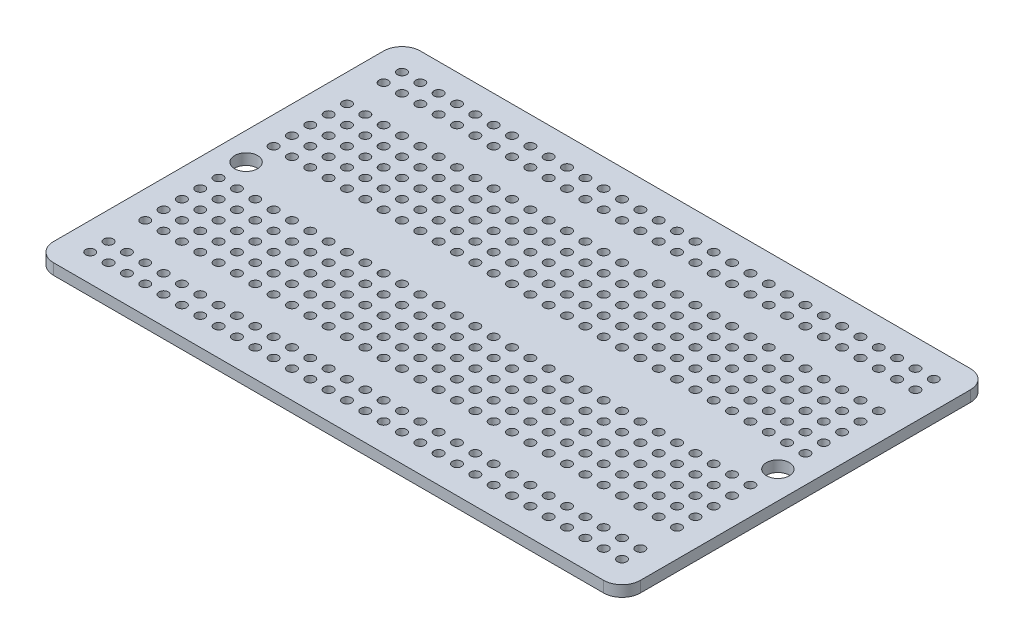
SolidWorks part; units mm, degrees
ref_plane "Front Plane" through (0, 0, 0) normal (0, 0, 1) x (1, 0, 0)
ref_plane "Top Plane" through (0, 0, 0) normal (0, 1, 0) x (1, 0, 0)
ref_plane "Right Plane" through (0, 0, 0) normal (1, 0, 0) x (0, 0, -1)
sketch "Sketch1" plane through (0, 0, 0) normal (0, 1, 0) x (1, 0, 0)
  line L0 (3.81, 46.99) -> (6.35, 46.99) construction
  line L1 (2.54, 0) -> (78.74, 0)
  line L2 (0, 2.54) -> (0, 48.26)
  line L3 (2.54, 50.8) -> (78.74, 50.8)
  line L4 (81.28, 2.54) -> (81.28, 48.26)
  line L5 (3.81, 44.45) -> (6.35, 44.45) construction
  line L6 (3.81, 41.91) -> (6.35, 41.91) construction
  line L7 (3.81, 39.37) -> (6.35, 39.37) construction
  line L8 (3.81, 36.83) -> (6.35, 36.83) construction
  line L9 (3.81, 34.29) -> (6.35, 34.29) construction
  line L10 (3.81, 31.75) -> (6.35, 31.75) construction
  line L11 (3.81, 29.21) -> (6.35, 29.21) construction
  line L12 (3.81, 26.67) -> (6.35, 26.67) construction
  line L13 (3.81, 24.13) -> (6.35, 24.13) construction
  line L14 (3.81, 21.59) -> (6.35, 21.59) construction
  line L15 (3.81, 19.05) -> (6.35, 19.05) construction
  line L16 (3.81, 16.51) -> (6.35, 16.51) construction
  line L17 (3.81, 13.97) -> (6.35, 13.97) construction
  line L18 (3.81, 11.43) -> (6.35, 11.43) construction
  line L19 (3.81, 8.89) -> (6.35, 8.89) construction
  line L20 (3.81, 6.35) -> (6.35, 6.35) construction
  line L21 (3.81, 3.81) -> (6.35, 3.81) construction
  line L22 (3.81, 46.99) -> (3.81, 44.45) construction
  arc A0 (78.74, 50.8) -> (81.28, 48.26) centre (78.74, 48.26) cw
  arc A1 (78.74, 0) -> (81.28, 2.54) centre (78.74, 2.54) ccw
  arc A2 (2.54, 0) -> (0, 2.54) centre (2.54, 2.54) cw
  arc A3 (0, 48.26) -> (2.54, 50.8) centre (2.54, 48.26) cw
  circle A4 centre (3.81, 46.99) radius 0.635
  circle A5 centre (6.35, 46.99) radius 0.635
  circle A6 centre (8.89, 46.99) radius 0.635
  circle A7 centre (11.43, 46.99) radius 0.635
  circle A8 centre (13.97, 46.99) radius 0.635
  circle A9 centre (16.51, 46.99) radius 0.635
  circle A10 centre (19.05, 46.99) radius 0.635
  circle A11 centre (21.59, 46.99) radius 0.635
  circle A12 centre (24.13, 46.99) radius 0.635
  circle A13 centre (26.67, 46.99) radius 0.635
  circle A14 centre (29.21, 46.99) radius 0.635
  circle A15 centre (31.75, 46.99) radius 0.635
  circle A16 centre (34.29, 46.99) radius 0.635
  circle A17 centre (36.83, 46.99) radius 0.635
  circle A18 centre (39.37, 46.99) radius 0.635
  circle A19 centre (41.91, 46.99) radius 0.635
  circle A20 centre (44.45, 46.99) radius 0.635
  circle A21 centre (46.99, 46.99) radius 0.635
  circle A22 centre (49.53, 46.99) radius 0.635
  circle A23 centre (52.07, 46.99) radius 0.635
  circle A24 centre (54.61, 46.99) radius 0.635
  circle A25 centre (57.15, 46.99) radius 0.635
  circle A26 centre (59.69, 46.99) radius 0.635
  circle A27 centre (62.23, 46.99) radius 0.635
  circle A28 centre (64.77, 46.99) radius 0.635
  circle A29 centre (67.31, 46.99) radius 0.635
  circle A30 centre (69.85, 46.99) radius 0.635
  circle A31 centre (72.39, 46.99) radius 0.635
  circle A32 centre (74.93, 46.99) radius 0.635
  circle A33 centre (77.47, 46.99) radius 0.635
  circle A34 centre (3.81, 44.45) radius 0.635
  circle A35 centre (6.35, 44.45) radius 0.635
  circle A36 centre (8.89, 44.45) radius 0.635
  circle A37 centre (11.43, 44.45) radius 0.635
  circle A38 centre (13.97, 44.45) radius 0.635
  circle A39 centre (16.51, 44.45) radius 0.635
  circle A40 centre (19.05, 44.45) radius 0.635
  circle A41 centre (21.59, 44.45) radius 0.635
  circle A42 centre (24.13, 44.45) radius 0.635
  circle A43 centre (26.67, 44.45) radius 0.635
  circle A44 centre (29.21, 44.45) radius 0.635
  circle A45 centre (31.75, 44.45) radius 0.635
  circle A46 centre (34.29, 44.45) radius 0.635
  circle A47 centre (36.83, 44.45) radius 0.635
  circle A48 centre (39.37, 44.45) radius 0.635
  circle A49 centre (41.91, 44.45) radius 0.635
  circle A50 centre (44.45, 44.45) radius 0.635
  circle A51 centre (46.99, 44.45) radius 0.635
  circle A52 centre (49.53, 44.45) radius 0.635
  circle A53 centre (52.07, 44.45) radius 0.635
  circle A54 centre (54.61, 44.45) radius 0.635
  circle A55 centre (57.15, 44.45) radius 0.635
  circle A56 centre (59.69, 44.45) radius 0.635
  circle A57 centre (62.23, 44.45) radius 0.635
  circle A58 centre (64.77, 44.45) radius 0.635
  circle A59 centre (67.31, 44.45) radius 0.635
  circle A60 centre (69.85, 44.45) radius 0.635
  circle A61 centre (72.39, 44.45) radius 0.635
  circle A62 centre (74.93, 44.45) radius 0.635
  circle A63 centre (77.47, 44.45) radius 0.635
  circle A64 centre (3.81, 41.91) radius 0.635 [skipped]
  circle A65 centre (6.35, 41.91) radius 0.635 [skipped]
  circle A66 centre (8.89, 41.91) radius 0.635 [skipped]
  circle A67 centre (11.43, 41.91) radius 0.635 [skipped]
  circle A68 centre (13.97, 41.91) radius 0.635 [skipped]
  circle A69 centre (16.51, 41.91) radius 0.635 [skipped]
  circle A70 centre (19.05, 41.91) radius 0.635 [skipped]
  circle A71 centre (21.59, 41.91) radius 0.635 [skipped]
  circle A72 centre (24.13, 41.91) radius 0.635 [skipped]
  circle A73 centre (26.67, 41.91) radius 0.635 [skipped]
  circle A74 centre (29.21, 41.91) radius 0.635 [skipped]
  circle A75 centre (31.75, 41.91) radius 0.635 [skipped]
  circle A76 centre (34.29, 41.91) radius 0.635 [skipped]
  circle A77 centre (36.83, 41.91) radius 0.635 [skipped]
  circle A78 centre (39.37, 41.91) radius 0.635 [skipped]
  circle A79 centre (41.91, 41.91) radius 0.635 [skipped]
  circle A80 centre (44.45, 41.91) radius 0.635 [skipped]
  circle A81 centre (46.99, 41.91) radius 0.635 [skipped]
  circle A82 centre (49.53, 41.91) radius 0.635 [skipped]
  circle A83 centre (52.07, 41.91) radius 0.635 [skipped]
  circle A84 centre (54.61, 41.91) radius 0.635 [skipped]
  circle A85 centre (57.15, 41.91) radius 0.635 [skipped]
  circle A86 centre (59.69, 41.91) radius 0.635 [skipped]
  circle A87 centre (62.23, 41.91) radius 0.635 [skipped]
  circle A88 centre (64.77, 41.91) radius 0.635 [skipped]
  circle A89 centre (67.31, 41.91) radius 0.635 [skipped]
  circle A90 centre (69.85, 41.91) radius 0.635 [skipped]
  circle A91 centre (72.39, 41.91) radius 0.635 [skipped]
  circle A92 centre (74.93, 41.91) radius 0.635 [skipped]
  circle A93 centre (77.47, 41.91) radius 0.635 [skipped]
  circle A94 centre (3.81, 39.37) radius 0.635
  circle A95 centre (6.35, 39.37) radius 0.635
  circle A96 centre (8.89, 39.37) radius 0.635
  circle A97 centre (11.43, 39.37) radius 0.635
  circle A98 centre (13.97, 39.37) radius 0.635
  circle A99 centre (16.51, 39.37) radius 0.635
  circle A100 centre (19.05, 39.37) radius 0.635
  circle A101 centre (21.59, 39.37) radius 0.635
  circle A102 centre (24.13, 39.37) radius 0.635
  circle A103 centre (26.67, 39.37) radius 0.635
  circle A104 centre (29.21, 39.37) radius 0.635
  circle A105 centre (31.75, 39.37) radius 0.635
  circle A106 centre (34.29, 39.37) radius 0.635
  circle A107 centre (36.83, 39.37) radius 0.635
  circle A108 centre (39.37, 39.37) radius 0.635
  circle A109 centre (41.91, 39.37) radius 0.635
  circle A110 centre (44.45, 39.37) radius 0.635
  circle A111 centre (46.99, 39.37) radius 0.635
  circle A112 centre (49.53, 39.37) radius 0.635
  circle A113 centre (52.07, 39.37) radius 0.635
  circle A114 centre (54.61, 39.37) radius 0.635
  circle A115 centre (57.15, 39.37) radius 0.635
  circle A116 centre (59.69, 39.37) radius 0.635
  circle A117 centre (62.23, 39.37) radius 0.635
  circle A118 centre (64.77, 39.37) radius 0.635
  circle A119 centre (67.31, 39.37) radius 0.635
  circle A120 centre (69.85, 39.37) radius 0.635
  circle A121 centre (72.39, 39.37) radius 0.635
  circle A122 centre (74.93, 39.37) radius 0.635
  circle A123 centre (77.47, 39.37) radius 0.635
  circle A124 centre (3.81, 36.83) radius 0.635
  circle A125 centre (6.35, 36.83) radius 0.635
  circle A126 centre (8.89, 36.83) radius 0.635
  circle A127 centre (11.43, 36.83) radius 0.635
  circle A128 centre (13.97, 36.83) radius 0.635
  circle A129 centre (16.51, 36.83) radius 0.635
  circle A130 centre (19.05, 36.83) radius 0.635
  circle A131 centre (21.59, 36.83) radius 0.635
  circle A132 centre (24.13, 36.83) radius 0.635
  circle A133 centre (26.67, 36.83) radius 0.635
  circle A134 centre (29.21, 36.83) radius 0.635
  circle A135 centre (31.75, 36.83) radius 0.635
  circle A136 centre (34.29, 36.83) radius 0.635
  circle A137 centre (36.83, 36.83) radius 0.635
  circle A138 centre (39.37, 36.83) radius 0.635
  circle A139 centre (41.91, 36.83) radius 0.635
  circle A140 centre (44.45, 36.83) radius 0.635
  circle A141 centre (46.99, 36.83) radius 0.635
  circle A142 centre (49.53, 36.83) radius 0.635
  circle A143 centre (52.07, 36.83) radius 0.635
  circle A144 centre (54.61, 36.83) radius 0.635
  circle A145 centre (57.15, 36.83) radius 0.635
  circle A146 centre (59.69, 36.83) radius 0.635
  circle A147 centre (62.23, 36.83) radius 0.635
  circle A148 centre (64.77, 36.83) radius 0.635
  circle A149 centre (67.31, 36.83) radius 0.635
  circle A150 centre (69.85, 36.83) radius 0.635
  circle A151 centre (72.39, 36.83) radius 0.635
  circle A152 centre (74.93, 36.83) radius 0.635
  circle A153 centre (77.47, 36.83) radius 0.635
  circle A154 centre (3.81, 34.29) radius 0.635
  circle A155 centre (6.35, 34.29) radius 0.635
  circle A156 centre (8.89, 34.29) radius 0.635
  circle A157 centre (11.43, 34.29) radius 0.635
  circle A158 centre (13.97, 34.29) radius 0.635
  circle A159 centre (16.51, 34.29) radius 0.635
  circle A160 centre (19.05, 34.29) radius 0.635
  circle A161 centre (21.59, 34.29) radius 0.635
  circle A162 centre (24.13, 34.29) radius 0.635
  circle A163 centre (26.67, 34.29) radius 0.635
  circle A164 centre (29.21, 34.29) radius 0.635
  circle A165 centre (31.75, 34.29) radius 0.635
  circle A166 centre (34.29, 34.29) radius 0.635
  circle A167 centre (36.83, 34.29) radius 0.635
  circle A168 centre (39.37, 34.29) radius 0.635
  circle A169 centre (41.91, 34.29) radius 0.635
  circle A170 centre (44.45, 34.29) radius 0.635
  circle A171 centre (46.99, 34.29) radius 0.635
  circle A172 centre (49.53, 34.29) radius 0.635
  circle A173 centre (52.07, 34.29) radius 0.635
  circle A174 centre (54.61, 34.29) radius 0.635
  circle A175 centre (57.15, 34.29) radius 0.635
  circle A176 centre (59.69, 34.29) radius 0.635
  circle A177 centre (62.23, 34.29) radius 0.635
  circle A178 centre (64.77, 34.29) radius 0.635
  circle A179 centre (67.31, 34.29) radius 0.635
  circle A180 centre (69.85, 34.29) radius 0.635
  circle A181 centre (72.39, 34.29) radius 0.635
  circle A182 centre (74.93, 34.29) radius 0.635
  circle A183 centre (77.47, 34.29) radius 0.635
  circle A184 centre (3.81, 31.75) radius 0.635
  circle A185 centre (6.35, 31.75) radius 0.635
  circle A186 centre (8.89, 31.75) radius 0.635
  circle A187 centre (11.43, 31.75) radius 0.635
  circle A188 centre (13.97, 31.75) radius 0.635
  circle A189 centre (16.51, 31.75) radius 0.635
  circle A190 centre (19.05, 31.75) radius 0.635
  circle A191 centre (21.59, 31.75) radius 0.635
  circle A192 centre (24.13, 31.75) radius 0.635
  circle A193 centre (26.67, 31.75) radius 0.635
  circle A194 centre (29.21, 31.75) radius 0.635
  circle A195 centre (31.75, 31.75) radius 0.635
  circle A196 centre (34.29, 31.75) radius 0.635
  circle A197 centre (36.83, 31.75) radius 0.635
  circle A198 centre (39.37, 31.75) radius 0.635
  circle A199 centre (41.91, 31.75) radius 0.635
  circle A200 centre (44.45, 31.75) radius 0.635
  circle A201 centre (46.99, 31.75) radius 0.635
  circle A202 centre (49.53, 31.75) radius 0.635
  circle A203 centre (52.07, 31.75) radius 0.635
  circle A204 centre (54.61, 31.75) radius 0.635
  circle A205 centre (57.15, 31.75) radius 0.635
  circle A206 centre (59.69, 31.75) radius 0.635
  circle A207 centre (62.23, 31.75) radius 0.635
  circle A208 centre (64.77, 31.75) radius 0.635
  circle A209 centre (67.31, 31.75) radius 0.635
  circle A210 centre (69.85, 31.75) radius 0.635
  circle A211 centre (72.39, 31.75) radius 0.635
  circle A212 centre (74.93, 31.75) radius 0.635
  circle A213 centre (77.47, 31.75) radius 0.635
  circle A214 centre (3.81, 29.21) radius 0.635
  circle A215 centre (6.35, 29.21) radius 0.635
  circle A216 centre (8.89, 29.21) radius 0.635
  circle A217 centre (11.43, 29.21) radius 0.635
  circle A218 centre (13.97, 29.21) radius 0.635
  circle A219 centre (16.51, 29.21) radius 0.635
  circle A220 centre (19.05, 29.21) radius 0.635
  circle A221 centre (21.59, 29.21) radius 0.635
  circle A222 centre (24.13, 29.21) radius 0.635
  circle A223 centre (26.67, 29.21) radius 0.635
  circle A224 centre (29.21, 29.21) radius 0.635
  circle A225 centre (31.75, 29.21) radius 0.635
  circle A226 centre (34.29, 29.21) radius 0.635
  circle A227 centre (36.83, 29.21) radius 0.635
  circle A228 centre (39.37, 29.21) radius 0.635
  circle A229 centre (41.91, 29.21) radius 0.635
  circle A230 centre (44.45, 29.21) radius 0.635
  circle A231 centre (46.99, 29.21) radius 0.635
  circle A232 centre (49.53, 29.21) radius 0.635
  circle A233 centre (52.07, 29.21) radius 0.635
  circle A234 centre (54.61, 29.21) radius 0.635
  circle A235 centre (57.15, 29.21) radius 0.635
  circle A236 centre (59.69, 29.21) radius 0.635
  circle A237 centre (62.23, 29.21) radius 0.635
  circle A238 centre (64.77, 29.21) radius 0.635
  circle A239 centre (67.31, 29.21) radius 0.635
  circle A240 centre (69.85, 29.21) radius 0.635
  circle A241 centre (72.39, 29.21) radius 0.635
  circle A242 centre (74.93, 29.21) radius 0.635
  circle A243 centre (77.47, 29.21) radius 0.635
  circle A244 centre (3.81, 26.67) radius 0.635 [skipped]
  circle A245 centre (6.35, 26.67) radius 0.635 [skipped]
  circle A246 centre (8.89, 26.67) radius 0.635 [skipped]
  circle A247 centre (11.43, 26.67) radius 0.635 [skipped]
  circle A248 centre (13.97, 26.67) radius 0.635 [skipped]
  circle A249 centre (16.51, 26.67) radius 0.635 [skipped]
  circle A250 centre (19.05, 26.67) radius 0.635 [skipped]
  circle A251 centre (21.59, 26.67) radius 0.635 [skipped]
  circle A252 centre (24.13, 26.67) radius 0.635 [skipped]
  circle A253 centre (26.67, 26.67) radius 0.635 [skipped]
  circle A254 centre (29.21, 26.67) radius 0.635 [skipped]
  circle A255 centre (31.75, 26.67) radius 0.635 [skipped]
  circle A256 centre (34.29, 26.67) radius 0.635 [skipped]
  circle A257 centre (36.83, 26.67) radius 0.635 [skipped]
  circle A258 centre (39.37, 26.67) radius 0.635 [skipped]
  circle A259 centre (41.91, 26.67) radius 0.635 [skipped]
  circle A260 centre (44.45, 26.67) radius 0.635 [skipped]
  circle A261 centre (46.99, 26.67) radius 0.635 [skipped]
  circle A262 centre (49.53, 26.67) radius 0.635 [skipped]
  circle A263 centre (52.07, 26.67) radius 0.635 [skipped]
  circle A264 centre (54.61, 26.67) radius 0.635 [skipped]
  circle A265 centre (57.15, 26.67) radius 0.635 [skipped]
  circle A266 centre (59.69, 26.67) radius 0.635 [skipped]
  circle A267 centre (62.23, 26.67) radius 0.635 [skipped]
  circle A268 centre (64.77, 26.67) radius 0.635 [skipped]
  circle A269 centre (67.31, 26.67) radius 0.635 [skipped]
  circle A270 centre (69.85, 26.67) radius 0.635 [skipped]
  circle A271 centre (72.39, 26.67) radius 0.635 [skipped]
  circle A272 centre (74.93, 26.67) radius 0.635 [skipped]
  circle A273 centre (77.47, 26.67) radius 0.635 [skipped]
  circle A274 centre (3.81, 24.13) radius 0.635 [skipped]
  circle A275 centre (6.35, 24.13) radius 0.635 [skipped]
  circle A276 centre (8.89, 24.13) radius 0.635 [skipped]
  circle A277 centre (11.43, 24.13) radius 0.635 [skipped]
  circle A278 centre (13.97, 24.13) radius 0.635 [skipped]
  circle A279 centre (16.51, 24.13) radius 0.635 [skipped]
  circle A280 centre (19.05, 24.13) radius 0.635 [skipped]
  circle A281 centre (21.59, 24.13) radius 0.635 [skipped]
  circle A282 centre (24.13, 24.13) radius 0.635 [skipped]
  circle A283 centre (26.67, 24.13) radius 0.635 [skipped]
  circle A284 centre (29.21, 24.13) radius 0.635 [skipped]
  circle A285 centre (31.75, 24.13) radius 0.635 [skipped]
  circle A286 centre (34.29, 24.13) radius 0.635 [skipped]
  circle A287 centre (36.83, 24.13) radius 0.635 [skipped]
  circle A288 centre (39.37, 24.13) radius 0.635 [skipped]
  circle A289 centre (41.91, 24.13) radius 0.635 [skipped]
  circle A290 centre (44.45, 24.13) radius 0.635 [skipped]
  circle A291 centre (46.99, 24.13) radius 0.635 [skipped]
  circle A292 centre (49.53, 24.13) radius 0.635 [skipped]
  circle A293 centre (52.07, 24.13) radius 0.635 [skipped]
  circle A294 centre (54.61, 24.13) radius 0.635 [skipped]
  circle A295 centre (57.15, 24.13) radius 0.635 [skipped]
  circle A296 centre (59.69, 24.13) radius 0.635 [skipped]
  circle A297 centre (62.23, 24.13) radius 0.635 [skipped]
  circle A298 centre (64.77, 24.13) radius 0.635 [skipped]
  circle A299 centre (67.31, 24.13) radius 0.635 [skipped]
  circle A300 centre (69.85, 24.13) radius 0.635 [skipped]
  circle A301 centre (72.39, 24.13) radius 0.635 [skipped]
  circle A302 centre (74.93, 24.13) radius 0.635 [skipped]
  circle A303 centre (77.47, 24.13) radius 0.635 [skipped]
  circle A304 centre (3.81, 21.59) radius 0.635
  circle A305 centre (6.35, 21.59) radius 0.635
  circle A306 centre (8.89, 21.59) radius 0.635
  circle A307 centre (11.43, 21.59) radius 0.635
  circle A308 centre (13.97, 21.59) radius 0.635
  circle A309 centre (16.51, 21.59) radius 0.635
  circle A310 centre (19.05, 21.59) radius 0.635
  circle A311 centre (21.59, 21.59) radius 0.635
  circle A312 centre (24.13, 21.59) radius 0.635
  circle A313 centre (26.67, 21.59) radius 0.635
  circle A314 centre (29.21, 21.59) radius 0.635
  circle A315 centre (31.75, 21.59) radius 0.635
  circle A316 centre (34.29, 21.59) radius 0.635
  circle A317 centre (36.83, 21.59) radius 0.635
  circle A318 centre (39.37, 21.59) radius 0.635
  circle A319 centre (41.91, 21.59) radius 0.635
  circle A320 centre (44.45, 21.59) radius 0.635
  circle A321 centre (46.99, 21.59) radius 0.635
  circle A322 centre (49.53, 21.59) radius 0.635
  circle A323 centre (52.07, 21.59) radius 0.635
  circle A324 centre (54.61, 21.59) radius 0.635
  circle A325 centre (57.15, 21.59) radius 0.635
  circle A326 centre (59.69, 21.59) radius 0.635
  circle A327 centre (62.23, 21.59) radius 0.635
  circle A328 centre (64.77, 21.59) radius 0.635
  circle A329 centre (67.31, 21.59) radius 0.635
  circle A330 centre (69.85, 21.59) radius 0.635
  circle A331 centre (72.39, 21.59) radius 0.635
  circle A332 centre (74.93, 21.59) radius 0.635
  circle A333 centre (77.47, 21.59) radius 0.635
  circle A334 centre (3.81, 19.05) radius 0.635
  circle A335 centre (6.35, 19.05) radius 0.635
  circle A336 centre (8.89, 19.05) radius 0.635
  circle A337 centre (11.43, 19.05) radius 0.635
  circle A338 centre (13.97, 19.05) radius 0.635
  circle A339 centre (16.51, 19.05) radius 0.635
  circle A340 centre (19.05, 19.05) radius 0.635
  circle A341 centre (21.59, 19.05) radius 0.635
  circle A342 centre (24.13, 19.05) radius 0.635
  circle A343 centre (26.67, 19.05) radius 0.635
  circle A344 centre (29.21, 19.05) radius 0.635
  circle A345 centre (31.75, 19.05) radius 0.635
  circle A346 centre (34.29, 19.05) radius 0.635
  circle A347 centre (36.83, 19.05) radius 0.635
  circle A348 centre (39.37, 19.05) radius 0.635
  circle A349 centre (41.91, 19.05) radius 0.635
  circle A350 centre (44.45, 19.05) radius 0.635
  circle A351 centre (46.99, 19.05) radius 0.635
  circle A352 centre (49.53, 19.05) radius 0.635
  circle A353 centre (52.07, 19.05) radius 0.635
  circle A354 centre (54.61, 19.05) radius 0.635
  circle A355 centre (57.15, 19.05) radius 0.635
  circle A356 centre (59.69, 19.05) radius 0.635
  circle A357 centre (62.23, 19.05) radius 0.635
  circle A358 centre (64.77, 19.05) radius 0.635
  circle A359 centre (67.31, 19.05) radius 0.635
  circle A360 centre (69.85, 19.05) radius 0.635
  circle A361 centre (72.39, 19.05) radius 0.635
  circle A362 centre (74.93, 19.05) radius 0.635
  circle A363 centre (77.47, 19.05) radius 0.635
  circle A364 centre (3.81, 16.51) radius 0.635
  circle A365 centre (6.35, 16.51) radius 0.635
  circle A366 centre (8.89, 16.51) radius 0.635
  circle A367 centre (11.43, 16.51) radius 0.635
  circle A368 centre (13.97, 16.51) radius 0.635
  circle A369 centre (16.51, 16.51) radius 0.635
  circle A370 centre (19.05, 16.51) radius 0.635
  circle A371 centre (21.59, 16.51) radius 0.635
  circle A372 centre (24.13, 16.51) radius 0.635
  circle A373 centre (26.67, 16.51) radius 0.635
  circle A374 centre (29.21, 16.51) radius 0.635
  circle A375 centre (31.75, 16.51) radius 0.635
  circle A376 centre (34.29, 16.51) radius 0.635
  circle A377 centre (36.83, 16.51) radius 0.635
  circle A378 centre (39.37, 16.51) radius 0.635
  circle A379 centre (41.91, 16.51) radius 0.635
  circle A380 centre (44.45, 16.51) radius 0.635
  circle A381 centre (46.99, 16.51) radius 0.635
  circle A382 centre (49.53, 16.51) radius 0.635
  circle A383 centre (52.07, 16.51) radius 0.635
  circle A384 centre (54.61, 16.51) radius 0.635
  circle A385 centre (57.15, 16.51) radius 0.635
  circle A386 centre (59.69, 16.51) radius 0.635
  circle A387 centre (62.23, 16.51) radius 0.635
  circle A388 centre (64.77, 16.51) radius 0.635
  circle A389 centre (67.31, 16.51) radius 0.635
  circle A390 centre (69.85, 16.51) radius 0.635
  circle A391 centre (72.39, 16.51) radius 0.635
  circle A392 centre (74.93, 16.51) radius 0.635
  circle A393 centre (77.47, 16.51) radius 0.635
  circle A394 centre (3.81, 13.97) radius 0.635
  circle A395 centre (6.35, 13.97) radius 0.635
  circle A396 centre (8.89, 13.97) radius 0.635
  circle A397 centre (11.43, 13.97) radius 0.635
  circle A398 centre (13.97, 13.97) radius 0.635
  circle A399 centre (16.51, 13.97) radius 0.635
  circle A400 centre (19.05, 13.97) radius 0.635
  circle A401 centre (21.59, 13.97) radius 0.635
  circle A402 centre (24.13, 13.97) radius 0.635
  circle A403 centre (26.67, 13.97) radius 0.635
  circle A404 centre (29.21, 13.97) radius 0.635
  circle A405 centre (31.75, 13.97) radius 0.635
  circle A406 centre (34.29, 13.97) radius 0.635
  circle A407 centre (36.83, 13.97) radius 0.635
  circle A408 centre (39.37, 13.97) radius 0.635
  circle A409 centre (41.91, 13.97) radius 0.635
  circle A410 centre (44.45, 13.97) radius 0.635
  circle A411 centre (46.99, 13.97) radius 0.635
  circle A412 centre (49.53, 13.97) radius 0.635
  circle A413 centre (52.07, 13.97) radius 0.635
  circle A414 centre (54.61, 13.97) radius 0.635
  circle A415 centre (57.15, 13.97) radius 0.635
  circle A416 centre (59.69, 13.97) radius 0.635
  circle A417 centre (62.23, 13.97) radius 0.635
  circle A418 centre (64.77, 13.97) radius 0.635
  circle A419 centre (67.31, 13.97) radius 0.635
  circle A420 centre (69.85, 13.97) radius 0.635
  circle A421 centre (72.39, 13.97) radius 0.635
  circle A422 centre (74.93, 13.97) radius 0.635
  circle A423 centre (77.47, 13.97) radius 0.635
  circle A424 centre (3.81, 11.43) radius 0.635
  circle A425 centre (6.35, 11.43) radius 0.635
  circle A426 centre (8.89, 11.43) radius 0.635
  circle A427 centre (11.43, 11.43) radius 0.635
  circle A428 centre (13.97, 11.43) radius 0.635
  circle A429 centre (16.51, 11.43) radius 0.635
  circle A430 centre (19.05, 11.43) radius 0.635
  circle A431 centre (21.59, 11.43) radius 0.635
  circle A432 centre (24.13, 11.43) radius 0.635
  circle A433 centre (26.67, 11.43) radius 0.635
  circle A434 centre (29.21, 11.43) radius 0.635
  circle A435 centre (31.75, 11.43) radius 0.635
  circle A436 centre (34.29, 11.43) radius 0.635
  circle A437 centre (36.83, 11.43) radius 0.635
  circle A438 centre (39.37, 11.43) radius 0.635
  circle A439 centre (41.91, 11.43) radius 0.635
  circle A440 centre (44.45, 11.43) radius 0.635
  circle A441 centre (46.99, 11.43) radius 0.635
  circle A442 centre (49.53, 11.43) radius 0.635
  circle A443 centre (52.07, 11.43) radius 0.635
  circle A444 centre (54.61, 11.43) radius 0.635
  circle A445 centre (57.15, 11.43) radius 0.635
  circle A446 centre (59.69, 11.43) radius 0.635
  circle A447 centre (62.23, 11.43) radius 0.635
  circle A448 centre (64.77, 11.43) radius 0.635
  circle A449 centre (67.31, 11.43) radius 0.635
  circle A450 centre (69.85, 11.43) radius 0.635
  circle A451 centre (72.39, 11.43) radius 0.635
  circle A452 centre (74.93, 11.43) radius 0.635
  circle A453 centre (77.47, 11.43) radius 0.635
  circle A454 centre (3.81, 8.89) radius 0.635 [skipped]
  circle A455 centre (6.35, 8.89) radius 0.635 [skipped]
  circle A456 centre (8.89, 8.89) radius 0.635 [skipped]
  circle A457 centre (11.43, 8.89) radius 0.635 [skipped]
  circle A458 centre (13.97, 8.89) radius 0.635 [skipped]
  circle A459 centre (16.51, 8.89) radius 0.635 [skipped]
  circle A460 centre (19.05, 8.89) radius 0.635 [skipped]
  circle A461 centre (21.59, 8.89) radius 0.635 [skipped]
  circle A462 centre (24.13, 8.89) radius 0.635 [skipped]
  circle A463 centre (26.67, 8.89) radius 0.635 [skipped]
  circle A464 centre (29.21, 8.89) radius 0.635 [skipped]
  circle A465 centre (31.75, 8.89) radius 0.635 [skipped]
  circle A466 centre (34.29, 8.89) radius 0.635 [skipped]
  circle A467 centre (36.83, 8.89) radius 0.635 [skipped]
  circle A468 centre (39.37, 8.89) radius 0.635 [skipped]
  circle A469 centre (41.91, 8.89) radius 0.635 [skipped]
  circle A470 centre (44.45, 8.89) radius 0.635 [skipped]
  circle A471 centre (46.99, 8.89) radius 0.635 [skipped]
  circle A472 centre (49.53, 8.89) radius 0.635 [skipped]
  circle A473 centre (52.07, 8.89) radius 0.635 [skipped]
  circle A474 centre (54.61, 8.89) radius 0.635 [skipped]
  circle A475 centre (57.15, 8.89) radius 0.635 [skipped]
  circle A476 centre (59.69, 8.89) radius 0.635 [skipped]
  circle A477 centre (62.23, 8.89) radius 0.635 [skipped]
  circle A478 centre (64.77, 8.89) radius 0.635 [skipped]
  circle A479 centre (67.31, 8.89) radius 0.635 [skipped]
  circle A480 centre (69.85, 8.89) radius 0.635 [skipped]
  circle A481 centre (72.39, 8.89) radius 0.635 [skipped]
  circle A482 centre (74.93, 8.89) radius 0.635 [skipped]
  circle A483 centre (77.47, 8.89) radius 0.635 [skipped]
  circle A484 centre (3.81, 6.35) radius 0.635
  circle A485 centre (6.35, 6.35) radius 0.635
  circle A486 centre (8.89, 6.35) radius 0.635
  circle A487 centre (11.43, 6.35) radius 0.635
  circle A488 centre (13.97, 6.35) radius 0.635
  circle A489 centre (16.51, 6.35) radius 0.635
  circle A490 centre (19.05, 6.35) radius 0.635
  circle A491 centre (21.59, 6.35) radius 0.635
  circle A492 centre (24.13, 6.35) radius 0.635
  circle A493 centre (26.67, 6.35) radius 0.635
  circle A494 centre (29.21, 6.35) radius 0.635
  circle A495 centre (31.75, 6.35) radius 0.635
  circle A496 centre (34.29, 6.35) radius 0.635
  circle A497 centre (36.83, 6.35) radius 0.635
  circle A498 centre (39.37, 6.35) radius 0.635
  circle A499 centre (41.91, 6.35) radius 0.635
  circle A500 centre (44.45, 6.35) radius 0.635
  circle A501 centre (46.99, 6.35) radius 0.635
  circle A502 centre (49.53, 6.35) radius 0.635
  circle A503 centre (52.07, 6.35) radius 0.635
  circle A504 centre (54.61, 6.35) radius 0.635
  circle A505 centre (57.15, 6.35) radius 0.635
  circle A506 centre (59.69, 6.35) radius 0.635
  circle A507 centre (62.23, 6.35) radius 0.635
  circle A508 centre (64.77, 6.35) radius 0.635
  circle A509 centre (67.31, 6.35) radius 0.635
  circle A510 centre (69.85, 6.35) radius 0.635
  circle A511 centre (72.39, 6.35) radius 0.635
  circle A512 centre (74.93, 6.35) radius 0.635
  circle A513 centre (77.47, 6.35) radius 0.635
  circle A514 centre (3.81, 3.81) radius 0.635
  circle A515 centre (6.35, 3.81) radius 0.635
  circle A516 centre (8.89, 3.81) radius 0.635
  circle A517 centre (11.43, 3.81) radius 0.635
  circle A518 centre (13.97, 3.81) radius 0.635
  circle A519 centre (16.51, 3.81) radius 0.635
  circle A520 centre (19.05, 3.81) radius 0.635
  circle A521 centre (21.59, 3.81) radius 0.635
  circle A522 centre (24.13, 3.81) radius 0.635
  circle A523 centre (26.67, 3.81) radius 0.635
  circle A524 centre (29.21, 3.81) radius 0.635
  circle A525 centre (31.75, 3.81) radius 0.635
  circle A526 centre (34.29, 3.81) radius 0.635
  circle A527 centre (36.83, 3.81) radius 0.635
  circle A528 centre (39.37, 3.81) radius 0.635
  circle A529 centre (41.91, 3.81) radius 0.635
  circle A530 centre (44.45, 3.81) radius 0.635
  circle A531 centre (46.99, 3.81) radius 0.635
  circle A532 centre (49.53, 3.81) radius 0.635
  circle A533 centre (52.07, 3.81) radius 0.635
  circle A534 centre (54.61, 3.81) radius 0.635
  circle A535 centre (57.15, 3.81) radius 0.635
  circle A536 centre (59.69, 3.81) radius 0.635
  circle A537 centre (62.23, 3.81) radius 0.635
  circle A538 centre (64.77, 3.81) radius 0.635
  circle A539 centre (67.31, 3.81) radius 0.635
  circle A540 centre (69.85, 3.81) radius 0.635
  circle A541 centre (72.39, 3.81) radius 0.635
  circle A542 centre (74.93, 3.81) radius 0.635
  circle A543 centre (77.47, 3.81) radius 0.635
  circle A544 centre (3.81, 25.4) radius 1.5875
  circle A545 centre (77.47, 25.4) radius 1.5875
  point P9 (81.28, 0)
  point P12 (0, 0)
  point P15 (0, 50.8)
  point P1138 (0, 0)
  point P1139 (0, 25.4)
  point P1140 (0, 0)
  point P1141 (0, 0)
  dimension "D3" = 2.54
  dimension "D4" = 1.27
  dimension "D11" = 3.175
  dimension "D1" = 81.28
  dimension "D2" = 50.8
  dimension "D5" = 3.81
  dimension "D6" = 3.81
  dimension "D7" = 2.54
  dimension "D10" = 2.54
  dimension "D8" = 30
  dimension "D9" = 18
extrude "Boss-Extrude1" add sketch "Sketch1" along normal blind 1.524
